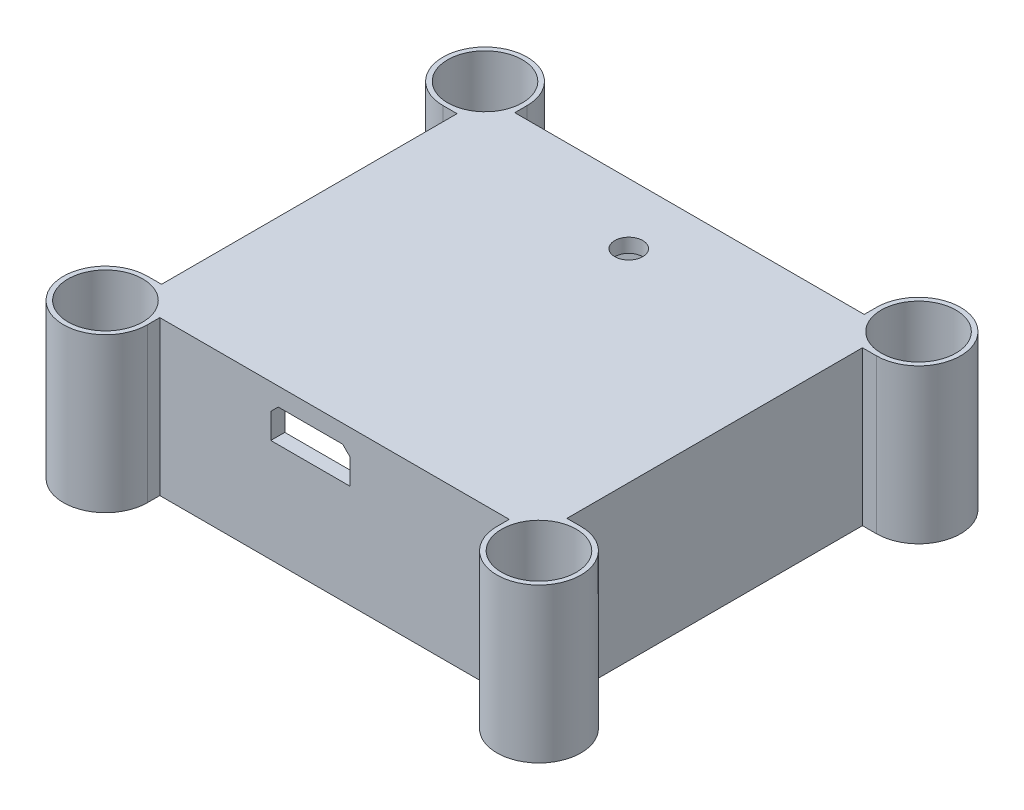
SolidWorks part; units mm, degrees
ref_plane "Front Plane" through (0, 0, 0) normal (0, 0, 1) x (1, 0, 0)
ref_plane "Top Plane" through (0, 0, 0) normal (0, 1, 0) x (1, 0, 0)
ref_plane "Right Plane" through (0, 0, 0) normal (1, 0, 0) x (0, 0, -1)
sketch "Sketch1" plane through (0, 0, 0) normal (0, 1, 0) x (1, 0, 0)
  line L0 (-20.2, 17.5) -> (-21.7, 17.5) construction
  line L1 (-20.2, 17.5) -> (20.2, 17.5)
  line L2 (-20.2, 17.5) -> (-20.2, -17.5)
  line L3 (-20.2, -17.5) -> (20.2, -17.5)
  line L4 (20.2, 17.5) -> (20.2, -17.5)
  line L5 (-20.2, 17.5) -> (20.2, -17.5) construction
  line L6 (-20.2, -17.5) -> (20.2, 17.5) construction
  line L7 (-20.2, 17.5) -> (20.2, 17.5)
  line L8 (-20.2, 17.5) -> (-20.2, 27.5)
  line L9 (-20.2, 27.5) -> (20.2, 27.5)
  line L10 (20.2, 17.5) -> (20.2, 27.5)
  line L11 (21.7, -19) -> (-21.7, -19)
  line L12 (21.7, -19) -> (21.7, 19)
  line L13 (21.7, 19) -> (-21.7, 19)
  line L14 (-21.7, -19) -> (-21.7, 19)
  line L15 (21.7, -19) -> (-21.7, 19) construction
  line L16 (21.7, 19) -> (-21.7, -19) construction
  line L17 (-20.2, 17.5) -> (-20.2, 19) construction
  line L18 (-23.2047, 15.8175) -> (-21.7, 15.8175)
  line L19 (-18.7047, 20.3175) -> (-18.7047, 19)
  line L20 (0, 19) -> (0, -19) construction
  line L21 (-21.7, 0) -> (21.7, 0) construction
  line L22 (18.7047, 20.3175) -> (18.7047, 19)
  line L23 (23.2047, 15.8175) -> (21.7, 15.8175)
  line L24 (18.7047, -20.3175) -> (18.7047, -19)
  line L25 (23.2047, -15.8175) -> (21.7, -15.8175)
  line L26 (-18.7047, -20.3175) -> (-18.7047, -19)
  line L27 (-23.2047, -15.8175) -> (-21.7, -15.8175)
  circle A0 centre (-23.2047, 20.3175) radius 2
  circle A1 centre (-23.2047, 20.3175) radius 4.5
  circle A2 centre (23.2047, 20.3175) radius 4.5
  circle A3 centre (23.2047, 20.3175) radius 2
  circle A4 centre (-23.2047, -20.3175) radius 2
  circle A5 centre (23.2047, -20.3175) radius 2
  circle A6 centre (23.2047, -20.3175) radius 4.5
  circle A7 centre (-23.2047, -20.3175) radius 4.5
  point P0 (0, 0)
  point P9 (0, 0)
  dimension "D5" = 4
  dimension "D6" = 9
  dimension "D1" = 40.4
  dimension "D2" = 35
  dimension "D3" = 10
  dimension "D4" = 1.5
extrude "Boss-Extrude1" add sketch "Sketch1" along normal blind 15 contours A7 L11 A4 L14 | L27 A7 L14 | A7 L14 L11 L3 L2 | L11 A7 L26 | L3 A7 L11 A6 | L14 A7 L2 A1 | A1 L14 A0 L13 L8 | L13 A1 L8 | L14 A1 L2 L8 L13 | L1 A1 L13 L8 | A1 L18 L14 | A1 L13 L19 | L7 A2 L13 A1 | L13 A3 L12 A2 L10 | L13 A2 L22 | A2 L1 L10 L13 | A2 L12 L13 L10 L4 | L23 A2 L12 | A6 L12 A2 L4 | A2 L13 L10 | L12 A6 L4 L3 L11 | A6 L25 L12 | A6 L12 A5 L11 | A6 L11 L24
sketch "Sketch2" plane through (0, 15, 0) normal (0, 1, 0) x (1, 0, 0)
  line L12 (-21.7, 15.8175) -> (-21.7, -15.8175)
  line L13 (-21.7, -15.8175) -> (-23.2047, -15.8175)
  line L14 (-18.7047, -20.3175) -> (-18.7047, -19)
  line L15 (-18.7047, -19) -> (18.7047, -19)
  line L16 (18.7047, -19) -> (18.7047, -20.3175)
  line L17 (23.2047, -15.8175) -> (21.7, -15.8175)
  line L18 (21.7, -15.8175) -> (21.7, 15.8175)
  line L19 (21.7, 15.8175) -> (23.2047, 15.8175)
  line L20 (18.7047, 20.3175) -> (18.7047, 19)
  line L21 (18.7047, 19) -> (-18.7047, 19)
  line L22 (-18.7047, 19) -> (-18.7047, 20.3175)
  line L23 (-23.2047, 15.8175) -> (-21.7, 15.8175)
  line L24 (-21.7, 15.8175) -> (-21.7, -15.8175)
  line L25 (-21.7, -15.8175) -> (-23.2047, -15.8175)
  line L26 (-18.7047, -20.3175) -> (-18.7047, -19)
  line L27 (-18.7047, -19) -> (18.7047, -19)
  line L28 (18.7047, -19) -> (18.7047, -20.3175)
  line L29 (23.2047, -15.8175) -> (21.7, -15.8175)
  line L30 (21.7, -15.8175) -> (21.7, 15.8175)
  line L31 (21.7, 15.8175) -> (23.2047, 15.8175)
  line L32 (18.7047, 20.3175) -> (18.7047, 19)
  line L33 (18.7047, 19) -> (-18.7047, 19)
  line L34 (-18.7047, 19) -> (-18.7047, 20.3175)
  line L35 (-23.2047, 15.8175) -> (-21.7, 15.8175)
  circle A0 centre (23.2047, -20.3175) radius 2 construction
  circle A1 centre (23.2047, 20.3175) radius 2 construction
  circle A2 centre (-23.2047, 20.3175) radius 2 construction
  circle A3 centre (-23.2047, -20.3175) radius 2 construction
  arc A4 (-23.2047, -15.8175) -> (-18.7047, -20.3175) centre (-23.2047, -20.3175) ccw
  arc A5 (18.7047, -20.3175) -> (23.2047, -15.8175) centre (23.2047, -20.3175) ccw
  arc A6 (23.2047, 15.8175) -> (18.7047, 20.3175) centre (23.2047, 20.3175) ccw
  arc A7 (-18.7047, 20.3175) -> (-23.2047, 15.8175) centre (-23.2047, 20.3175) ccw
  arc A8 (-23.2047, -15.8175) -> (-18.7047, -20.3175) centre (-23.2047, -20.3175) ccw
  arc A9 (18.7047, -20.3175) -> (23.2047, -15.8175) centre (23.2047, -20.3175) ccw
  arc A10 (23.2047, 15.8175) -> (18.7047, 20.3175) centre (23.2047, 20.3175) ccw
  arc A11 (-18.7047, 20.3175) -> (-23.2047, 15.8175) centre (-23.2047, 20.3175) ccw
  circle A12 centre (23.2047, -20.3175) radius 2
  circle A13 centre (23.2047, 20.3175) radius 2
  circle A14 centre (-23.2047, 20.3175) radius 2
  circle A15 centre (-23.2047, -20.3175) radius 2
  dimension "D1" = 0
extrude "Boss-Extrude2" add sketch "Sketch2" along normal blind 1.5
sketch "Sketch3" plane through (0, 16.5, 0) normal (0, 1, 0) x (1, 0, 0)
  circle A0 centre (-23.2047, -20.3175) radius 4
  arc A1 (-23.2047, -15.8175) -> (-18.7047, -20.3175) centre (-23.2047, -20.3175) ccw construction
  circle A2 centre (-23.2047, 20.3175) radius 4
  circle A3 centre (23.2047, 20.3175) radius 4
  circle A4 centre (23.2047, -20.3175) radius 4
  dimension "D1" = 0.5
extrude "Cut-Extrude1" cut sketch "Sketch3" against normal offset from surface (15 mm away) 1.5 up to face at (0, 0, 0)
sketch "Sketch4" plane through (0, 15, 0) normal (0, -1, 0) x (1, 0, 0)
  line L0 (-20.2, 17.5) -> (20.2, 17.5) construction
  line L1 (-7.2, 17.5) -> (2.05, 17.5)
  line L2 (-7.2, 17.5) -> (-7.2, 13.7)
  line L3 (-7.2, 13.7) -> (2.05, 13.7)
  line L4 (2.05, 17.5) -> (2.05, 13.7)
  line L5 (-7.2, 13.7) -> (-20.2, 13.7)
  line L6 (-20.2, -17.5) -> (-20.2, 17.5) construction
  line L7 (2.05, 13.7) -> (20.2, 13.7)
  line L8 (20.2, 17.5) -> (20.2, -17.5) construction
  line L9 (-20.2, -17.5) -> (-20.2, 17.5) construction
  line L10 (-20.2, -17.5) -> (20.2, -17.5) construction
  line L11 (-20.2, -17.5) -> (-17.2, -17.5)
  line L12 (-20.2, -17.5) -> (-20.2, -14.5)
  line L13 (-20.2, -14.5) -> (-17.2, -14.5)
  line L14 (-17.2, -17.5) -> (-17.2, -14.5)
  line L15 (14.45, -17.5) -> (11.95, -17.5)
  line L16 (14.45, -17.5) -> (14.45, -15.5)
  line L17 (14.45, -15.5) -> (11.95, -15.5)
  line L18 (11.95, -17.5) -> (11.95, -15.5)
  line L19 (20.2, 17.5) -> (20.2, -17.5) construction
  point P14 (-7.2, 15.6)
  dimension "D1" = 9.25
  dimension "D2" = 3.8
  dimension "D3" = 13
  dimension "D4" = 3
  dimension "D5" = 5.75
  dimension "D6" = 2.5
  dimension "D7" = 2
extrude "Boss-Extrude3" add sketch "Sketch4" along normal blind 1.1
sketch "Sketch5" plane through (0, 13.9, 0) normal (0, -1, 0) x (1, 0, 0)
  line L1 (-17.2, -17.5) -> (-20.2, -17.5)
  line L2 (-17.2, -17.5) -> (-17.2, -14)
  line L3 (-17.2, -14) -> (-20.2, -14)
  line L4 (-20.2, -17.5) -> (-20.2, -14)
  line L5 (-20.2, -14.5) -> (-17.2, -14.5) construction
  line L6 (11.95, -17.5) -> (11.95, -15.5) construction
  line L7 (14.45, -17.5) -> (11.95, -17.5)
  line L8 (14.45, -17.5) -> (14.45, -15)
  line L9 (14.45, -15) -> (11.95, -15)
  line L10 (11.95, -17.5) -> (11.95, -15)
  line L11 (-18.7, -14) -> (-18.7, -14.5) construction
  line L12 (13.2, -15) -> (13.2, -15.5) construction
  line L13 (14.45, -15.5) -> (11.95, -15.5) construction
  line L14 (-13.7, 17.5) -> (-13.7, 13.7) construction
  line L15 (-7.2, 17.5) -> (-20.2, 17.5) construction
  line L16 (-7.2, 13.7) -> (-20.2, 13.7) construction
  line L17 (-20.2, 17.5) -> (20.2, 17.5) construction
  line L18 (-15.2, 17.5) -> (-12.2, 17.5)
  line L19 (-15.2, 17.5) -> (-15.2, 13.2)
  line L20 (-15.2, 13.2) -> (-12.2, 13.2)
  line L21 (-12.2, 17.5) -> (-12.2, 13.2)
  line L22 (-15.2, 17.5) -> (-12.2, 13.2) construction
  line L23 (-15.2, 13.2) -> (-12.2, 17.5) construction
  line L24 (-13.7, 13.7) -> (-13.7, 13.2) construction
  line L25 (11.125, 17.5) -> (11.125, 13.7) construction
  line L26 (20.2, 17.5) -> (2.05, 17.5) construction
  line L27 (2.05, 13.7) -> (20.2, 13.7) construction
  line L28 (11.125, 13.7) -> (11.125, 13.2) construction
  line L29 (9.625, 17.5) -> (12.625, 17.5)
  line L30 (9.625, 17.5) -> (9.625, 13.2)
  line L31 (9.625, 13.2) -> (12.625, 13.2)
  line L32 (12.625, 17.5) -> (12.625, 13.2)
  line L33 (9.625, 17.5) -> (12.625, 13.2) construction
  line L34 (9.625, 13.2) -> (12.625, 17.5) construction
  line L35 (-20.2, -17.5) -> (-17.2, -17.5) construction
  point P5 (0, 0)
  point P6 (-20.2, -12.45)
  point P28 (-13.7, 15.35)
  point P42 (11.125, 15.35)
  point P47 (0, 0)
  point P49 (0, 0)
  point P50 (0, 0)
  dimension "D1" = 0.5
  dimension "D2" = 3
extrude "Boss-Extrude4" add sketch "Sketch5" along normal blind 1
chamfer "Chamfer1" distance 0.5 angle 45 2 edges at (-18.7, 12.9, -14) (13.2, 12.9, -15)
sketch "Sketch6" plane through (0, 0, 17.5) normal (0, 0, -1) x (-1, 0, 0)
  line L0 (7.2, 15) -> (-2.05, 15) construction
  line L1 (2.575, 15) -> (2.575, 0) construction
  line L2 (20.2, 0) -> (-20.2, 0) construction
  line L4 (-1.675, 11.05) -> (6.825, 11.05)
  line L5 (-1.675, 11.05) -> (-1.675, 14.55)
  line L6 (-1.675, 14.55) -> (6.825, 14.55)
  line L7 (6.825, 11.05) -> (6.825, 14.55)
  line L8 (-1.675, 11.05) -> (6.825, 14.55) construction
  line L9 (-1.675, 14.55) -> (6.825, 11.05) construction
  point P6 (2.575, 12.8)
  dimension "D1" = 8.5
  dimension "D2" = 3.5
  dimension "D3" = 3.95
extrude "Cut-Extrude2" cut sketch "Sketch6" against normal up to next
chamfer "Chamfer2" distance 0.8 angle 45 2 edges at (-6.825, 14.55, 18.25) (1.675, 14.55, 18.25)
fillet "Fillet1" radius 2 4 edges at (20.2, 7.5, -17.5) (-20.2, 6.45, -17.5) (-20.2, 6.95, 17.5) (20.2, 6.95, 17.5)
sketch "Sketch7" plane through (0, 15, 0) normal (0, -1, 0) x (1, 0, 0)
  line L0 (-20.2, -12.5) -> (20.2, -12.5) construction
  line L1 (-20.2, -14.5) -> (-20.2, 13.7) construction
  line L2 (20.2, 13.7) -> (20.2, -15.5) construction
  line L3 (-17.2, -17.5) -> (11.95, -17.5) construction
  circle A0 centre (0, -12.5) radius 1.5
  dimension "D1" = 3
  dimension "D2" = 5
extrude "Cut-Extrude3" cut sketch "Sketch7" against normal up to next
